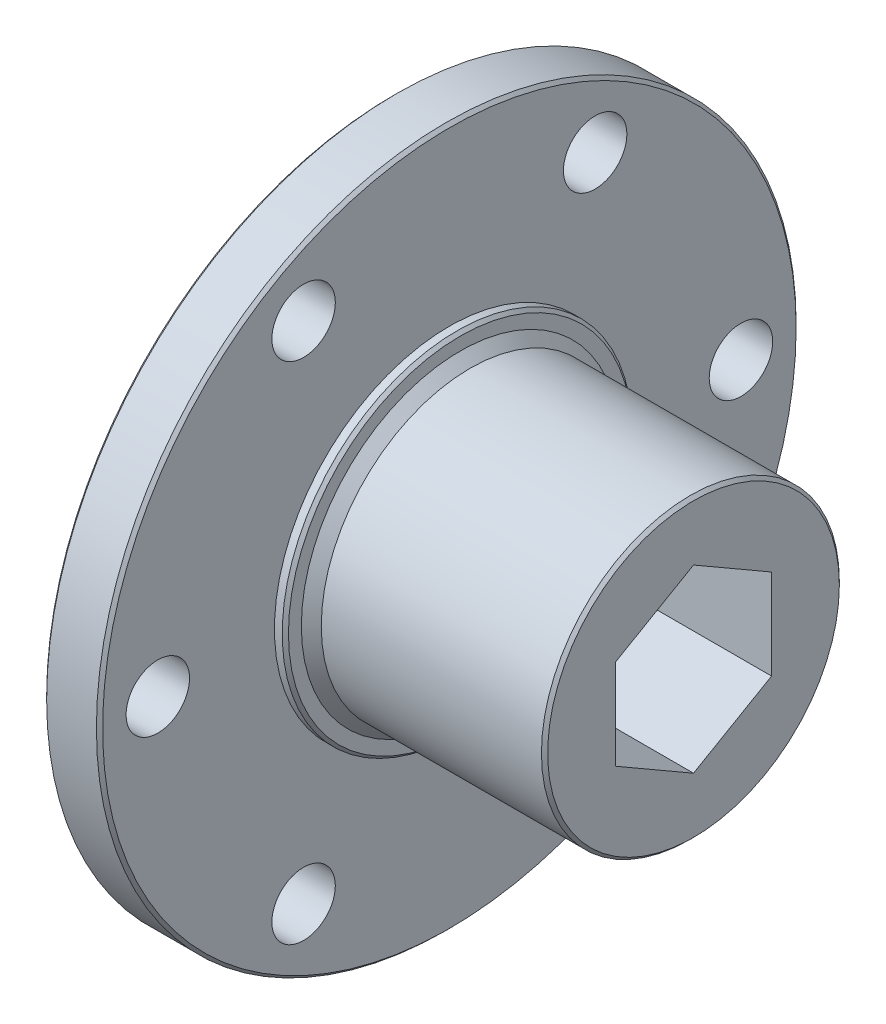
SolidWorks part; units mm, degrees
ref_plane "Front Plane" through (0, 0, 0) normal (0, 0, 1) x (1, 0, 0)
ref_plane "Top Plane" through (0, 0, 0) normal (0, 1, 0) x (1, 0, 0)
ref_plane "Right Plane" through (0, 0, 0) normal (1, 0, 0) x (0, 0, -1)
ref_plane "Plane1" through (0, 0, 0) normal (0, 0, -1) x (-1, 0, 0)
sketch "Sketch1" plane through (0, 0, 0) normal (0, 0, -1) x (-1, 0, 0)
  line L0 (13.9241, 28.575) -> (13.9241, 0)
  line L1 (13.9241, 0) -> (18.4961, 0)
  line L2 (18.4961, 0) -> (18.4961, 28.575)
  line L3 (18.4961, 28.575) -> (13.9241, 28.575)
  line L4 (13.9241, 0) -> (18.4961, 0) construction
revolve "Revolve1" add sketch "Sketch1" angle 360 about L4
sketch "Sketch2" plane through (-13.9241, 0, 0) normal (1, 0, 0) x (0, 0, -1)
  circle A0 centre (0, 0) radius 14.2875
extrude "Boss-Extrude1" add sketch "Sketch2" along normal blind 0.889
sketch "Sketch3" plane through (-13.0351, 0, 0) normal (1, 0, 0) x (0, 0, -1)
  circle A0 centre (0, 0) radius 12.9794
extrude "Boss-Extrude2" add sketch "Sketch3" along normal blind 0.8128 draft 45
sketch "Sketch4" plane through (-12.2223, 0, 0) normal (1, 0, 0) x (0, 0, -1)
  circle A0 centre (0, 0) radius 12.1666
extrude "Boss-Extrude3" add sketch "Sketch4" along normal blind 18.2372
sketch "Sketch5" plane through (-18.4961, 0, 0) normal (-1, 0, 0) x (0, 0, 1)
  circle A0 centre (0, 0) radius 14.2875
extrude "Boss-Extrude4" add sketch "Sketch5" along normal blind 0.889
sketch "Sketch6" plane through (-19.3851, 0, 0) normal (-1, 0, 0) x (0, 0, 1)
  line L0 (0, 7.3617) -> (-6.3754, 3.6808)
  line L1 (-6.3754, 3.6808) -> (-6.3754, -3.6809)
  line L2 (-6.3754, -3.6809) -> (0, -7.3617)
  line L3 (0, -7.3617) -> (6.3754, -3.6809)
  line L4 (6.3754, -3.6809) -> (6.3754, 3.6808)
  line L5 (6.3754, 3.6808) -> (0, 7.3617)
extrude "Cut-Extrude1" cut sketch "Sketch6" against normal through all
hole_wizard "#6 (0.204) Diameter Hole1" positions "Sketch8" profile "Sketch7" hole size "#6" standard "ANSI Inch"
sketch "Sketch8" plane through (-18.4961, 0, 0) normal (-1, 0, 0) x (0, 0, 1)
  point P0 (11.9063, 20.6222)
  point P1 (-23.8125, 0)
  point P2 (11.9062, -20.6222)
  point P3 (-11.9063, -20.6222)
  point P4 (-11.9062, 20.6222)
  point P5 (23.8125, 0)
sketch "Sketch7" plane through (-18.4961, 20.6222, 11.9063) normal (0, 1, 0) x (0, 0, 1)
  line L0 (0, 0) -> (0, 24.511)
  line L1 (0, 24.511) -> (2.5908, 24.511)
  line L2 (2.5908, 24.511) -> (2.5908, 0)
  line L5 (2.5908, 0) -> (0, 0)
  line L11 (0, -6.35) -> (0, 107.95) construction
  dimension "Thru Hole Dia." = 5.1816
  dimension "Thru Hole Depth" = 24.511
chamfer "Chamfer1" distance 0.254 angle 45 5 edges at (-19.3851, 0, 14.2875) (6.0149, 0, -12.1666) (-18.4961, 0, 28.575) (-13.0351, 0, -14.2875) (-13.9241, 0, 28.575)
